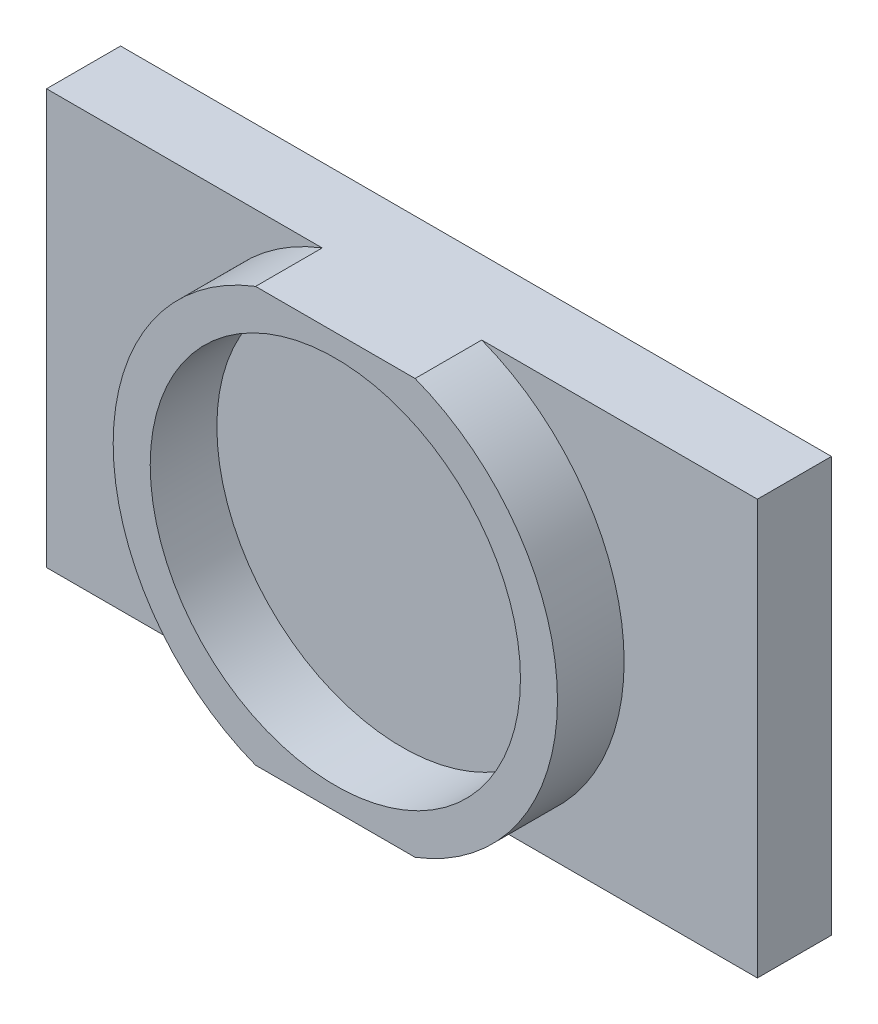
SolidWorks part; units mm, degrees
ref_plane "Front Plane" through (0, 0, 0) normal (0, 0, 1) x (1, 0, 0)
ref_plane "Top Plane" through (0, 0, 0) normal (0, 1, 0) x (1, 0, 0)
ref_plane "Right Plane" through (0, 0, 0) normal (1, 0, 0) x (0, 0, -1)
sketch "Sketch1" plane through (0, 0, 0) normal (0, 0, 1) x (1, 0, 0)
  line L1 (-60.96, -35.56) -> (60.96, -35.56)
  line L2 (-60.96, -35.56) -> (-60.96, 35.56)
  line L3 (-60.96, 35.56) -> (60.96, 35.56)
  line L4 (60.96, -35.56) -> (60.96, 35.56)
  line L5 (-60.96, -35.56) -> (60.96, 35.56) construction
  line L6 (-60.96, 35.56) -> (60.96, -35.56) construction
  arc A0 (-13.6783, 35.56) -> (-13.6783, -35.56) centre (0, 0) ccw
  circle A1 centre (0, 0) radius 31.75
  arc A2 (13.6783, -35.56) -> (13.6783, 35.56) centre (0, 0) ccw
  point P0 (0, 0)
  dimension "D3" = 76.2
  dimension "D4" = 63.5
  dimension "D1" = 121.92
  dimension "D2" = 71.12
sketch "Sketch2" plane through (0, 0, 0) normal (0, 0, 1) x (1, 0, 0)
  line L0 (-60.96, -35.56) -> (-60.96, 35.56) construction
  line L1 (-60.96, 35.56) -> (60.96, 35.56) construction
  line L2 (60.96, -35.56) -> (60.96, 35.56) construction
  line L3 (-60.96, -35.56) -> (60.96, -35.56) construction
  line L4 (-60.96, -35.56) -> (-60.96, 35.56)
  line L5 (-60.96, 35.56) -> (60.96, 35.56)
  line L6 (60.96, -35.56) -> (60.96, 35.56)
  line L7 (-60.96, -35.56) -> (60.96, -35.56)
extrude "Boss-Extrude1" add sketch "Sketch2" against normal blind 12.7
sketch "Sketch3" plane through (0, 0, 0) normal (0, 0, 1) x (1, 0, 0)
  line L0 (-60.96, 35.56) -> (60.96, 35.56) construction
  line L1 (-60.96, -35.56) -> (60.96, -35.56) construction
  line L2 (-13.6783, 35.56) -> (13.6783, 35.56)
  line L3 (-13.6783, -35.56) -> (13.6783, -35.56)
  arc A0 (-13.6783, 35.56) -> (-13.6783, -35.56) centre (0, 0) ccw construction
  arc A1 (13.6783, -35.56) -> (13.6783, 35.56) centre (0, 0) ccw construction
  circle A2 centre (0, 0) radius 31.75 construction
  arc A3 (-13.6783, 35.56) -> (-13.6783, -35.56) centre (0, 0) ccw
  arc A4 (13.6783, -35.56) -> (13.6783, 35.56) centre (0, 0) ccw
  circle A5 centre (0, 0) radius 31.75
extrude "Boss-Extrude2" add sketch "Sketch3" along normal blind 11.43
